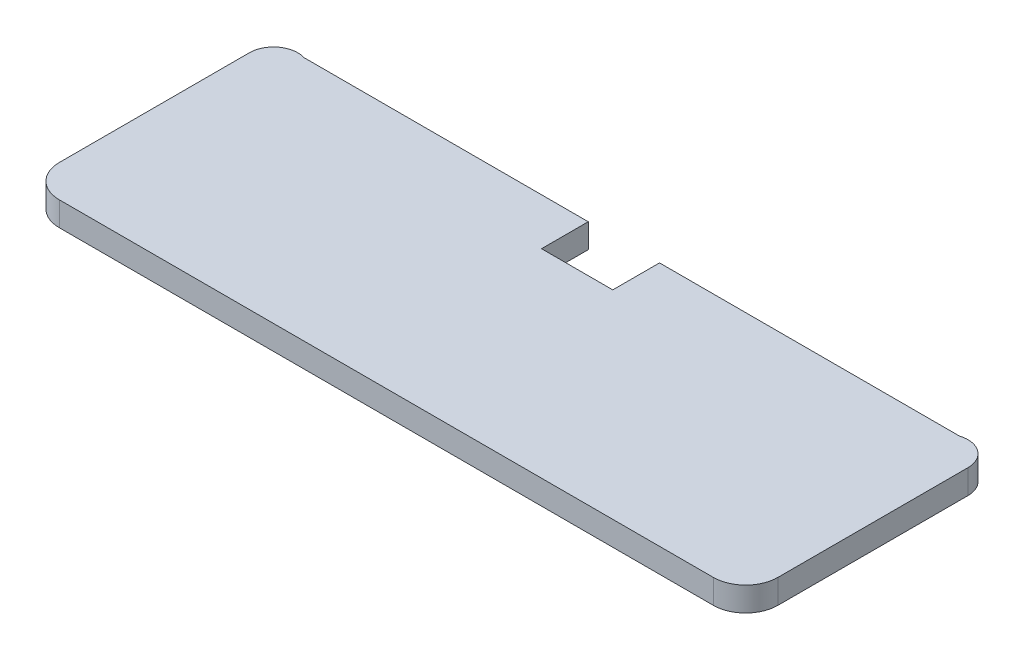
SolidWorks part; units mm, degrees
ref_plane "Plano frontal" through (0, 0, 0) normal (0, 0, 1) x (1, 0, 0)
ref_plane "Plano superior" through (0, 0, 0) normal (0, 1, 0) x (1, 0, 0)
ref_plane "Plano direito" through (0, 0, 0) normal (1, 0, 0) x (0, 0, -1)
sketch "Esboço1" plane through (0, 0, 0) normal (0, 1, 0) x (1, 0, 0)
  line L0 (37.1636, 16.4845) -> (0, 16.4845)
  line L1 (-8.8277, 16.4845) -> (-44.0364, 16.4845)
  line L2 (-47.9364, -9.9167) -> (-47.9364, 4.0833)
  line L3 (-47.9364, 13.6227) -> (-47.9364, 4.0833)
  line L4 (41.0636, 13.6227) -> (41.0636, 4.0833)
  line L6 (41.0636, -9.9167) -> (41.0636, 4.0833)
  line L7 (0, 16.4845) -> (0, 10.6951)
  line L8 (37.0636, -13.9167) -> (-43.9364, -13.9167)
  line L9 (0, 10.6951) -> (-8.8277, 10.6951)
  line L10 (-8.8277, 16.4845) -> (-8.8277, 10.6951)
  arc A0 (41.0636, 13.6227) -> (37.1636, 16.4845) centre (38.0636, 13.6227) ccw
  arc A1 (41.0636, -9.9167) -> (37.0636, -13.9167) centre (37.0636, -9.9167) cw
  arc A2 (-47.9364, -9.9167) -> (-43.9364, -13.9167) centre (-43.9364, -9.9167) ccw
  arc A3 (-47.9364, 13.6227) -> (-44.0364, 16.4845) centre (-44.9364, 13.6227) cw
  point P18 (41.0636, 17.0833)
  point P19 (-47.9364, 17.0833)
  dimension "D1" = 4
extrude "Ressalto-extrusão1" add sketch "Esboço1" along normal blind 3
